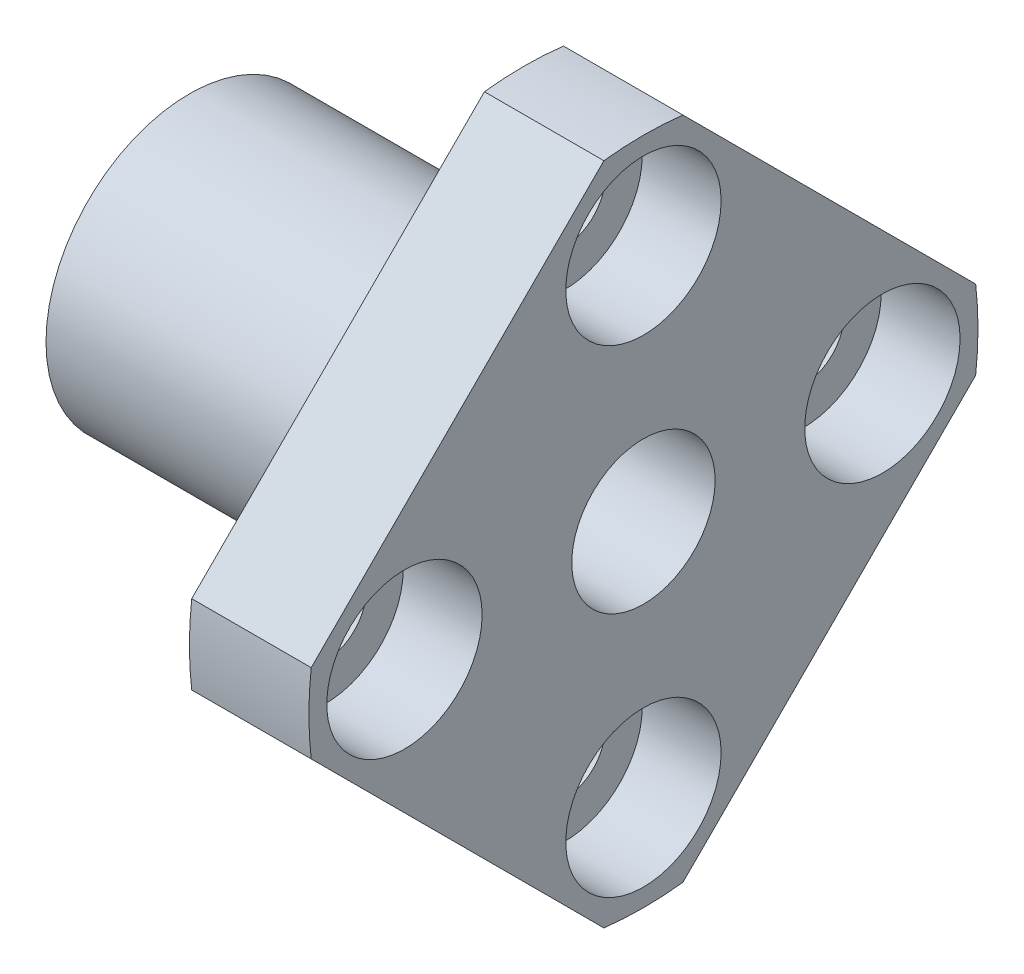
SolidWorks part; units mm, degrees
ref_plane "Front Plane" through (0, 0, 0) normal (0, 0, 1) x (1, 0, 0)
ref_plane "Top Plane" through (0, 0, 0) normal (0, 1, 0) x (1, 0, 0)
ref_plane "Right Plane" through (0, 0, 0) normal (1, 0, 0) x (0, 0, -1)
ref_plane "Plane1" through (14, 0, 0) normal (-1, 0, 0) x (0, -1, 0)
sketch "Sketch1" plane through (14, 0, 0) normal (-1, 0, 0) x (0, -1, 0)
  line L0 (-1.6545, 13.9019) -> (-13.9019, 1.6545)
  line L1 (-13.9019, -1.6545) -> (-1.6545, -13.9019)
  line L2 (1.6545, -13.9019) -> (13.9019, -1.6545)
  line L3 (13.9019, 1.6545) -> (1.6545, 13.9019)
  line L4 (-14, 0) -> (14, 0) construction
  arc A0 (-13.9019, 1.6545) -> (-13.9019, -1.6545) centre (0, 0) ccw
  arc A1 (-1.6545, -13.9019) -> (1.6545, -13.9019) centre (0, 0) ccw
  arc A2 (13.9019, -1.6545) -> (13.9019, 1.6545) centre (0, 0) ccw
  arc A3 (1.6545, 13.9019) -> (-1.6545, 13.9019) centre (0, 0) ccw
  dimension "D1" = 14
  dimension "D2" = 22
extrude "Boss-Extrude1" add sketch "Sketch1" against normal blind 5
ref_plane "Plane2" through (0, 0, 0) normal (0, 0, -1) x (-1, 0, 0)
sketch "Sketch2" plane through (0, 0, 0) normal (0, 0, -1) x (-1, 0, 0)
  line L0 (-14, 6) -> (-14, 0)
  line L1 (-14, 0) -> (0, 0)
  line L2 (0, 0) -> (0, 6)
  line L3 (0, 6) -> (-14, 6)
  line L4 (-14, 0) -> (0, 0) construction
  line L6 (-14, -1.6545) -> (-14, 1.6545) construction
  dimension "D1" = 14
  dimension "D2" = 6
revolve "Revolve1" add sketch "Sketch2" angle 360 about L4
hole_wizard "Ø6.0 (6) Diameter Hole1" positions "Sketch4" profile "Sketch3" hole size "Ø6.0" standard "ANSI Metric"
sketch "Sketch4" plane through (19, 0, 0) normal (1, 0, 0) x (0, 0, -1)
  point P0 (0, 0)
sketch "Sketch3" plane through (19, 0, 0) normal (0, 1, 0) x (0, 0, -1)
  line L0 (0, 0) -> (0, 19)
  line L1 (0, 19) -> (3, 19)
  line L2 (3, 19) -> (3, 0)
  line L5 (3, 0) -> (0, 0)
  line L11 (0, -6.35) -> (0, 107.95) construction
  dimension "Thru Hole Dia." = 6
  dimension "Thru Hole Depth" = 19
hole_wizard "CBORE for M3 Hex Head Machine Screw1" positions "Sketch6" profile "Sketch5" counterbore size "M3" standard "ANSI Metric"
sketch "Sketch6" plane through (19, 0, 0) normal (1, 0, 0) x (0, 0, -1)
  point P0 (0, -10)
  point P1 (10, 0)
  point P2 (-10, 0)
  point P3 (0, 10)
  point P9 (10, 0)
  point P10 (0, 0)
  dimension "D1" = 10
  dimension "D2" = 10
  dimension "D3" = 10
sketch "Sketch5" plane through (19, -10, 0) normal (0, 1, 0) x (0, 0, -1)
  line L0 (0, 0) -> (0, 19)
  line L1 (0, 19) -> (1.7, 19)
  line L3 (1.7, 19) -> (1.7, 3.3)
  line L4 (1.7, 3.3) -> (3.25, 3.3)
  line L5 (3.25, 3.3) -> (3.25, 0)
  line L7 (3.25, 0) -> (0, 0)
  line L11 (0, -6.35) -> (0, 107.95) construction
  dimension "Thru Hole Dia." = 3.4
  dimension "Thru Hole Depth" = 19
  dimension "C'Bore Dia." = 6.5
  dimension "C'Bore Depth" = 3.3
